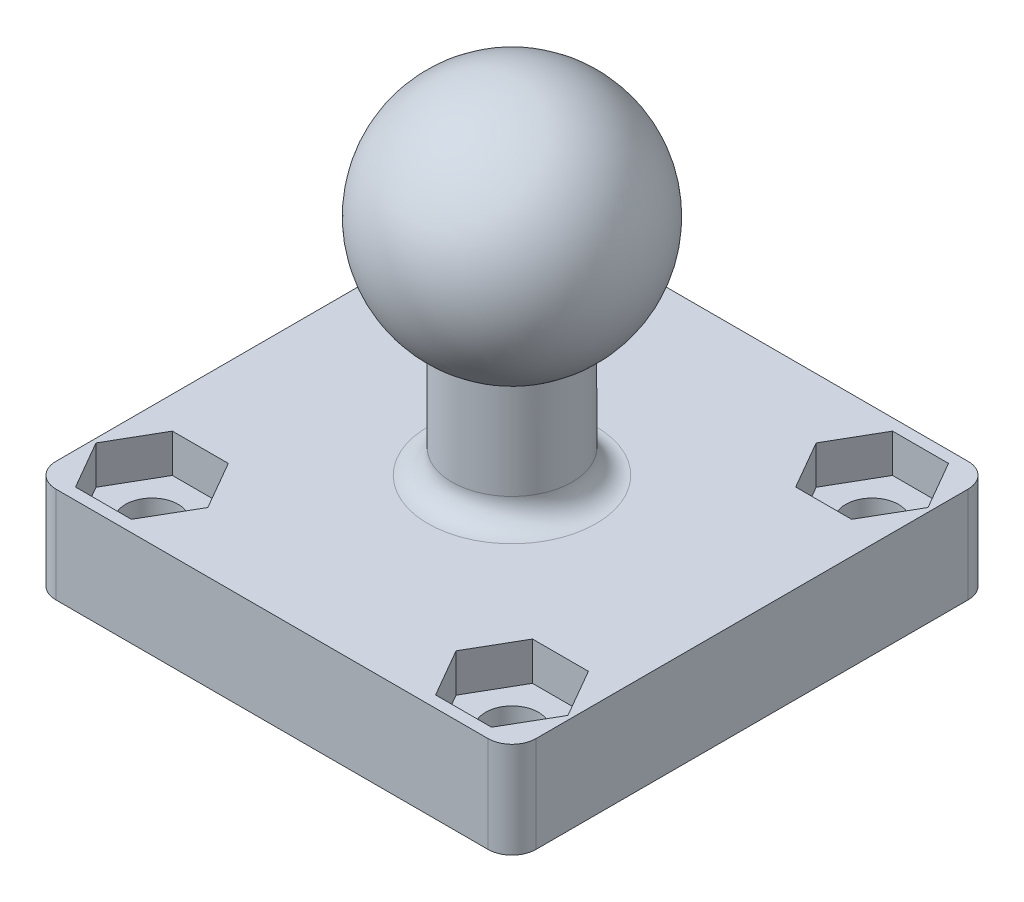
SolidWorks part; units mm, degrees
ref_plane "Plan de face" through (0, 0, 0) normal (0, 0, 1) x (1, 0, 0)
ref_plane "Plan de dessus" through (0, 0, 0) normal (0, 1, 0) x (1, 0, 0)
ref_plane "Plan de droite" through (0, 0, 0) normal (1, 0, 0) x (0, 0, -1)
sketch "Esquisse1" plane through (0, 0, 0) normal (0, 0, 1) x (1, 0, 0)
  line L0 (-2.5, -4.3301) -> (-2.5, -9.3301)
  line L1 (-2.5, -9.3301) -> (0, -9.3301)
  line L2 (0, -9.3301) -> (0, 5)
  line L3 (0, 5) -> (-7.2649, 5) construction
  arc A0 (0, 5) -> (-2.5, -4.3301) centre (0, 0) ccw
  dimension "D1" = 5
  dimension "D2" = 5
  dimension "D3" = 2.5
revolve "Révolution1" add sketch "Esquisse1" angle 360 about L2
sketch "Esquisse2" plane through (0, -9.3301, 0) normal (0, -1, 0) x (1, 0, 0)
  line L1 (-10, 10) -> (10, 10)
  line L2 (-10, 10) -> (-10, -10)
  line L3 (-10, -10) -> (10, -10)
  line L4 (10, 10) -> (10, -10)
  circle A0 centre (0, 0) radius 2.5 construction
  dimension "D3" = 10
  dimension "D4" = 10
  dimension "D1" = 20
  dimension "D2" = 20
extrude "Boss.-Extru.1" add sketch "Esquisse2" along normal blind 4
sketch "Esquisse3" plane through (0, -9.3301, 0) normal (0, 1, 0) x (1, 0, 0)
  circle A0 centre (7.5, -7.5) radius 1.1
  circle A1 centre (7.5, 7.5) radius 1.1
  circle A2 centre (-7.5, 7.5) radius 1.1
  circle A3 centre (-7.5, -7.5) radius 1.1
  circle A4 centre (0, 0) radius 2.5 construction
  dimension "D1" = 2.2
  dimension "D2" = 15
  dimension "D3" = 15
  dimension "D4" = 7.5
  dimension "D5" = 7.5
extrude "Enlèv. mat.-Extru.1" cut sketch "Esquisse3" against normal up to next
fillet "Congé1" radius 1 5 edges at (-10, -11.3301, -10) (2.5, -9.3301, 0) (10, -11.3301, -10) (10, -11.3301, 10) (-10, -11.3301, 10)
sketch "Esquisse4" plane through (0, -9.3301, 0) normal (0, 1, 0) x (1, 0, 0)
  line L0 (-9, 10) -> (9, 10) construction
  line L1 (-6.335, -5.4822) -> (-8.665, -5.4822)
  line L2 (-8.665, -5.4822) -> (-9.83, -7.5)
  line L3 (-9.83, -7.5) -> (-8.665, -9.5178)
  line L4 (-8.665, -9.5178) -> (-6.335, -9.5178)
  line L5 (-6.335, -9.5178) -> (-5.17, -7.5)
  line L6 (-5.17, -7.5) -> (-6.335, -5.4822)
  line L7 (9.83, -7.5) -> (8.665, -5.4822)
  line L8 (8.665, -5.4822) -> (6.335, -5.4822)
  line L9 (6.335, -5.4822) -> (5.17, -7.5)
  line L10 (5.17, -7.5) -> (6.335, -9.5178)
  line L11 (6.335, -9.5178) -> (8.665, -9.5178)
  line L12 (8.665, -9.5178) -> (9.83, -7.5)
  line L13 (8.665, 5.4822) -> (9.83, 7.5)
  line L14 (9.83, 7.5) -> (8.665, 9.5178)
  line L15 (8.665, 9.5178) -> (6.335, 9.5178)
  line L16 (6.335, 9.5178) -> (5.17, 7.5)
  line L17 (5.17, 7.5) -> (6.335, 5.4822)
  line L18 (6.335, 5.4822) -> (8.665, 5.4822)
  line L19 (-5.17, 7.5) -> (-6.335, 9.5178)
  line L20 (-6.335, 9.5178) -> (-8.665, 9.5178)
  line L21 (-8.665, 9.5178) -> (-9.83, 7.5)
  line L22 (-9.83, 7.5) -> (-8.665, 5.4822)
  line L23 (-8.665, 5.4822) -> (-6.335, 5.4822)
  line L24 (-6.335, 5.4822) -> (-5.17, 7.5)
  line L27 (9, -10) -> (-9, -10) construction
  circle A0 centre (-7.5, -7.5) radius 2.0178 construction
  circle A1 centre (7.5, -7.5) radius 2.0178 construction
  circle A2 centre (7.5, 7.5) radius 2.0178 construction
  circle A3 centre (-7.5, 7.5) radius 2.0178 construction
  dimension "D1" = 2.33
  dimension "D2" = 2.33
  dimension "D3" = 2.33
  dimension "D4" = 2.33
extrude "Enlèv. mat.-Extru.2" cut sketch "Esquisse4" against normal blind 1.6
